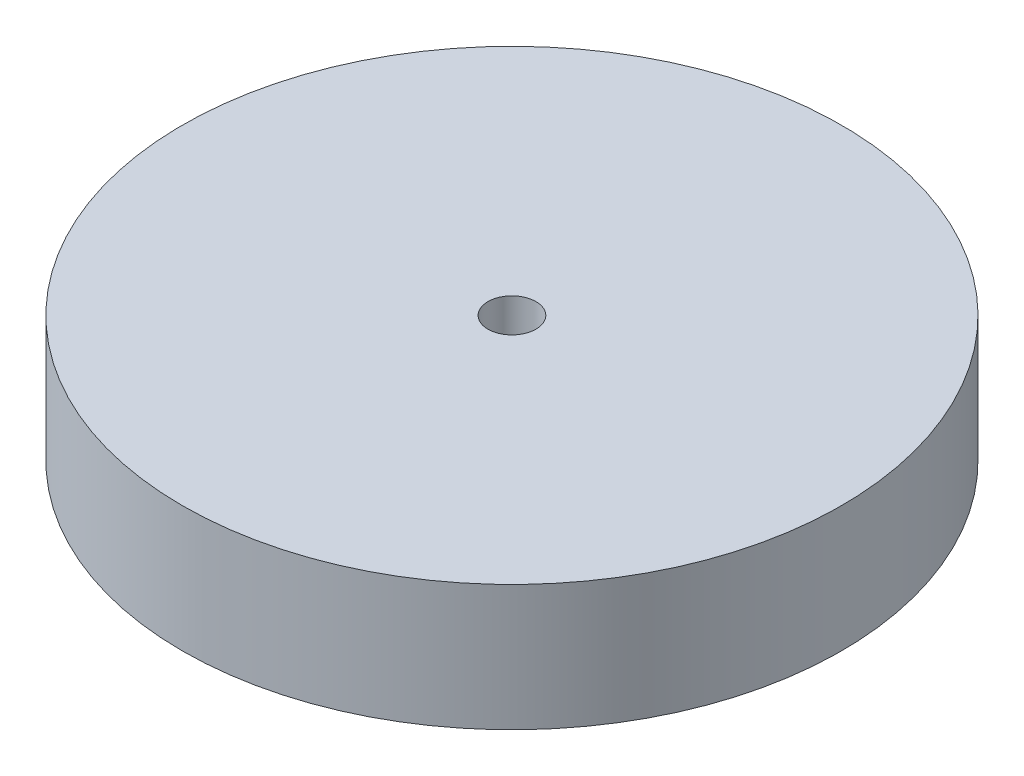
SolidWorks part; units mm, degrees
ref_plane "Front Plane" through (0, 0, 0) normal (0, 0, 1) x (1, 0, 0)
ref_plane "Top Plane" through (0, 0, 0) normal (0, 1, 0) x (1, 0, 0)
ref_plane "Right Plane" through (0, 0, 0) normal (1, 0, 0) x (0, 0, -1)
sketch "Sketch1" plane through (0, 0, 0) normal (0, 1, 0) x (1, 0, 0)
  circle A0 centre (0, 0) radius 55
  circle A1 centre (0, 0) radius 4
  dimension "D1" = 110
  dimension "D2" = 8
extrude "Boss-Extrude1" add sketch "Sketch1" along normal blind 21
